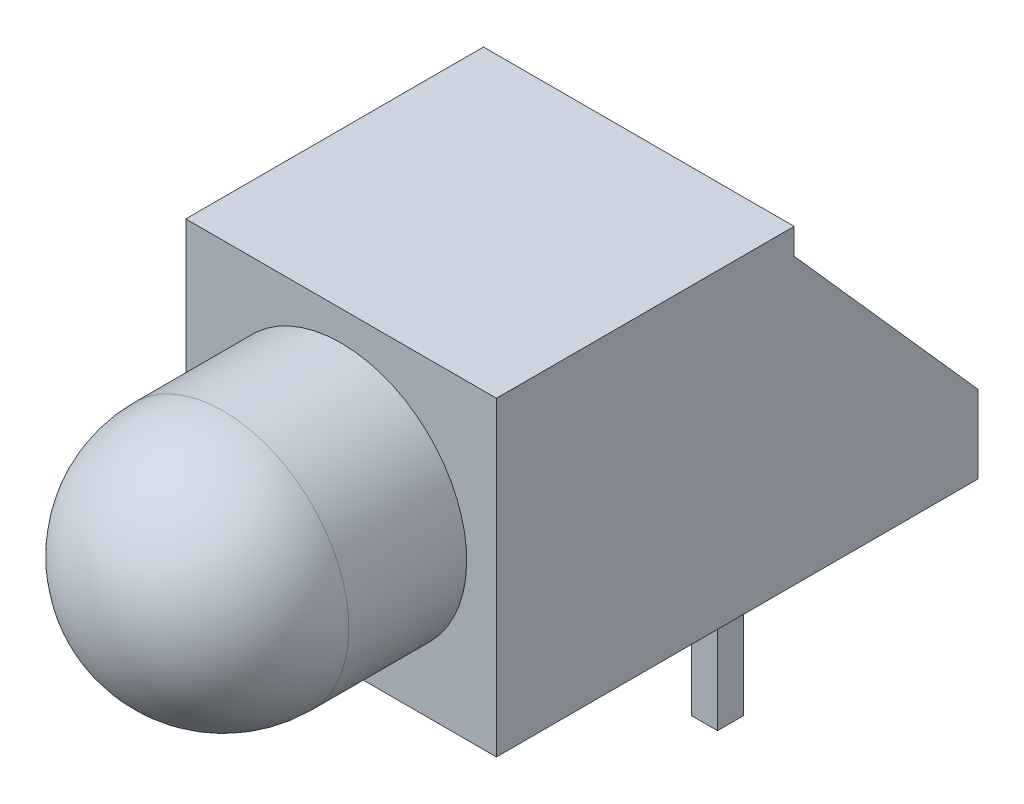
SolidWorks part; units mm, degrees
ref_plane "Front Plane" through (0, 0, 0) normal (0, 0, 1) x (1, 0, 0)
ref_plane "Top Plane" through (0, 0, 0) normal (0, 1, 0) x (1, 0, 0)
ref_plane "Right Plane" through (0, 0, 0) normal (1, 0, 0) x (0, 0, -1)
sketch "Sketch1" plane through (0, 0, 0) normal (1, 0, 0) x (0, 0, -1)
  line L0 (-6, 6) -> (-6, 0)
  line L1 (-6, 0) -> (3.3, 0)
  line L3 (-0.25, 6) -> (-6, 6)
  line L4 (-0.25, 6) -> (-0.25, 5.5)
  line L5 (-0.25, 5.5) -> (3.3, 1.5)
  line L6 (3.3, 1.5) -> (3.3, 0)
  line L7 (-0.25, 0) -> (-0.25, -3.175) construction
  line L8 (-0.25, -3.175) -> (0.25, -3.175) construction
  line L9 (0.25, -3.175) -> (0.25, 0) construction
  line L10 (-0.25, 0) -> (-0.25, 5.5) construction
  line L11 (0, 0) -> (0, -3.175) construction
  dimension "D1" = 6
  dimension "D2" = 9.3
  dimension "D3" = 5.75
  dimension "D4" = 0.5
  dimension "D5" = 3.175
  dimension "D6" = 1.5
  dimension "D7" = 0.5
extrude "Boss-Extrude1" add sketch "Sketch1" along normal mid plane 6
sketch "Sketch2" plane through (0, 0, 0) normal (1, 0, 0) x (0, 0, -1)
  line L0 (-6, 3) -> (-10.7, 3)
  line L1 (-6, 6) -> (-6, 0) construction
  line L2 (-6, 3) -> (-6, 5.425)
  line L3 (-6, 5.425) -> (-8.275, 5.425)
  line L4 (-6, 0.575) -> (-6, 5.425) construction
  arc A0 (-8.275, 5.425) -> (-10.7, 3) centre (-8.275, 3) ccw
  dimension "D1" = 4.85
  dimension "D2" = 4.7
revolve "Revolve1" add sketch "Sketch2" angle 360 about L0
sketch "Sketch3" plane through (0, 0, 0) normal (0, -1, 0) x (1, 0, 0)
  line L0 (-1.27, 0) -> (1.27, 0) construction
  line L1 (-1.27, 0.25) -> (-1.27, -0.25) construction
  line L2 (-1.52, 0.25) -> (-1.02, 0.25)
  line L3 (-1.52, 0.25) -> (-1.52, -0.25)
  line L4 (-1.52, -0.25) -> (-1.02, -0.25)
  line L5 (-1.02, 0.25) -> (-1.02, -0.25)
  line L6 (1.52, 0.25) -> (1.02, 0.25)
  line L7 (1.52, 0.25) -> (1.52, -0.25)
  line L8 (1.52, -0.25) -> (1.02, -0.25)
  line L9 (1.02, 0.25) -> (1.02, -0.25)
  line L10 (1.27, 0.25) -> (1.27, -0.25) construction
  point P14 (0, 0)
  dimension "D1" = 0.5
  dimension "D2" = 2.54
extrude "Boss-Extrude2" add sketch "Sketch3" along normal blind 3.175
